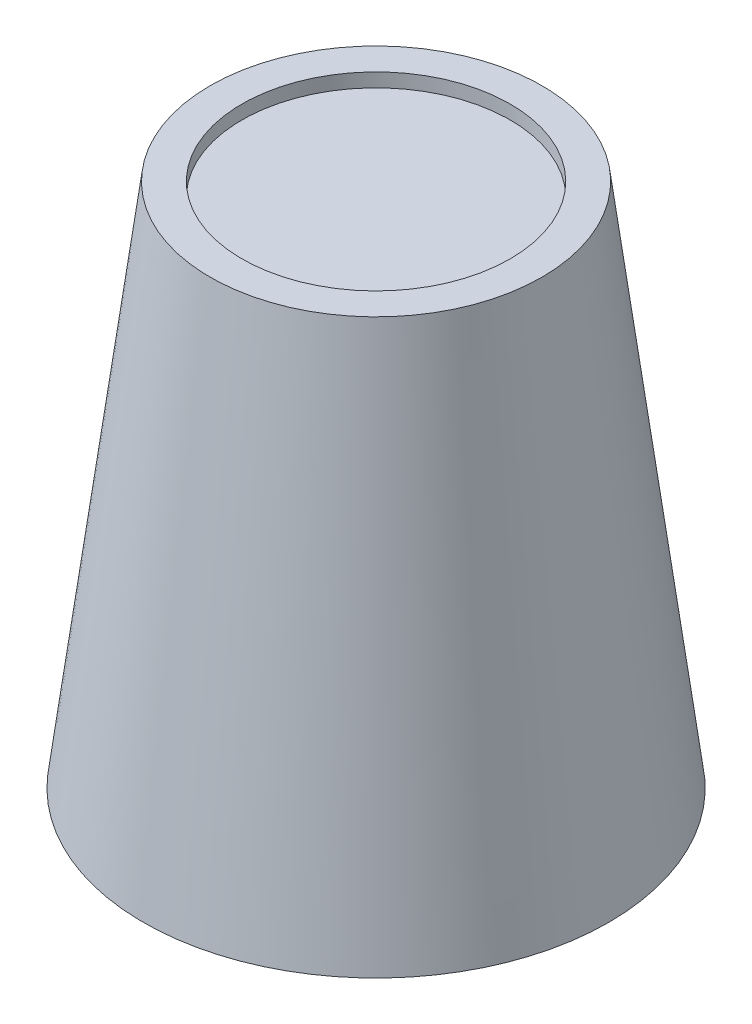
SolidWorks part; units mm, degrees
ref_plane "Спереди" through (0, 0, 0) normal (0, 0, 1) x (1, 0, 0)
ref_plane "Сверху" through (0, 0, 0) normal (0, 1, 0) x (1, 0, 0)
ref_plane "Справа" through (0, 0, 0) normal (1, 0, 0) x (0, 0, -1)
sketch "Эскиз2" plane through (0, 0, 0) normal (0, 0, 1) x (1, 0, 0)
  line L0 (0, 9.8464) -> (0, 9.3464)
  line L1 (6, -8.6536) -> (8.417, -8.6536)
  line L2 (8.417, -8.6536) -> (6, 10.3464)
  line L3 (6, 10.3464) -> (4.8518, 10.3464)
  line L4 (6, -8.6536) -> (6, -5.1536)
  line L5 (6, -5.1536) -> (2.5, -5.1536)
  line L6 (1.5, -3.1536) -> (1.5, 9.3464)
  line L7 (1.5, 9.3464) -> (0, 9.3464)
  line L8 (0, -1000) -> (0, 49000) construction
  line L9 (1.5, -3.1536) -> (2.5, -3.1536)
  line L10 (2.5, -3.1536) -> (2.5, -5.1536)
  line L11 (0, 9.8464) -> (4.8518, 9.8464)
  line L12 (4.8518, 9.8464) -> (4.8518, 10.3464)
  dimension "D1" = 19
  dimension "D2" = 6
  dimension "D4" = 1
  dimension "D5" = 3
  dimension "D6" = 12.5
  dimension "D7" = 2
revolve "Повернуть1" add sketch "Эскиз2" angle 360 about L8
